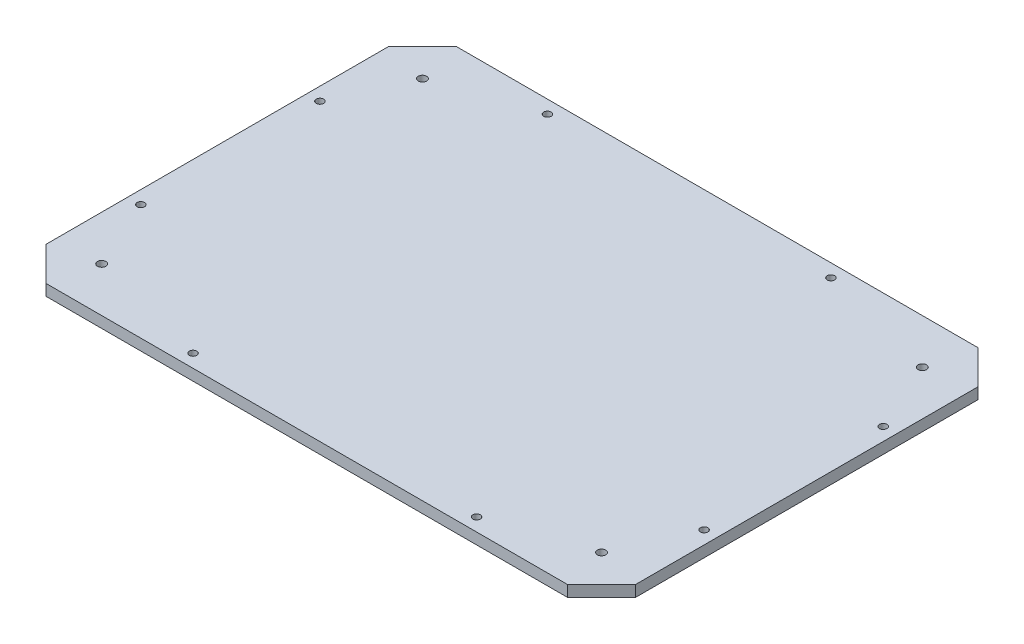
SolidWorks part; units mm, degrees
ref_plane "Front Plane" through (0, 0, 0) normal (0, 0, 1) x (1, 0, 0)
ref_plane "Top Plane" through (0, 0, 0) normal (0, 1, 0) x (1, 0, 0)
ref_plane "Right Plane" through (0, 0, 0) normal (1, 0, 0) x (0, 0, -1)
sketch "Sketch1" plane through (0, 0, 0) normal (0, 1, 0) x (1, 0, 0)
  line L1 (8.4883, 0) -> (510.1383, 0)
  line L2 (8.4883, 0) -> (8.4883, -349.25)
  line L3 (8.4883, -349.25) -> (510.1383, -349.25)
  line L4 (510.1383, 0) -> (510.1383, -349.25)
  dimension "D1" = 501.65
  dimension "D2" = 349.25
extrude "Boss-Extrude1" add sketch "Sketch1" along normal blind 9.525
sketch "Sketch2" plane through (0, 9.525, 0) normal (0, 1, 0) x (1, 0, 0)
  circle A0 centre (392.6633, -338.1375) radius 3.175
  circle A1 centre (151.3633, -338.1375) radius 3.175
  circle A2 centre (367.2633, -11.1125) radius 3.175
  circle A3 centre (125.9633, -11.1125) radius 3.175
  circle A4 centre (19.6008, -250.825) radius 3.175
  circle A5 centre (19.6008, -98.425) radius 3.175
  circle A6 centre (499.0258, -250.825) radius 3.175
  circle A7 centre (499.0258, -98.425) radius 3.175
extrude "Cut-Extrude1" cut sketch "Sketch2" against normal up to surface (9.525 mm away) up to face at (259.3133, 0, 174.625)
sketch "Sketch3" plane through (0, 9.525, 0) normal (0, 1, 0) x (1, 0, 0)
  line L0 (472.0383, -349.25) -> (472.0383, 3.175) construction
  line L1 (510.1383, -349.25) -> (8.4883, -349.25) construction
  line L2 (513.3133, 3.175) -> (5.3133, 3.175) construction
  line L3 (510.1383, 0) -> (510.1383, -349.25) construction
  line L4 (46.5883, -349.25) -> (46.5883, 0) construction
  line L5 (8.4883, 0) -> (510.1383, 0) construction
  line L6 (8.4883, -349.25) -> (8.4883, 0) construction
  line L7 (510.1383, -311.15) -> (8.4883, -311.15) construction
  line L8 (510.1383, -38.1) -> (8.4883, -38.1) construction
  point P18 (472.0383, -311.15)
  point P19 (472.0383, -38.1)
  point P20 (46.5883, -38.1)
  point P21 (46.5883, -311.15)
  dimension "D1" = 38.1
  dimension "D2" = 38.1
  dimension "D3" = 38.1
  dimension "D4" = 38.1
sketch "Sketch4" plane through (0, 9.525, 0) normal (0, 1, 0) x (1, 0, 0)
  circle A0 centre (472.0383, -38.1) radius 3.5719
  circle A1 centre (472.0383, -311.15) radius 3.5719
  circle A2 centre (46.5883, -311.15) radius 3.5719
  circle A3 centre (46.5883, -38.1) radius 3.5719
  dimension "D1" = 7.1437
  dimension "D2" = 7.1437
  dimension "D3" = 7.1437
  dimension "D4" = 7.1437
extrude "Cut-Extrude2" cut sketch "Sketch4" against normal up to surface (9.525 mm away) up to face at (499.0258, 0, 101.6)
chamfer "Chamfer1" distance 2.921 angle 42 4 edges at (46.5883, 0, 314.7219) (46.5883, 0, 41.6719) (472.0383, 0, 41.6719) (472.0383, 0, 314.7219)
sketch "Sketch5" plane through (0, 9.525, 0) normal (0, 1, 0) x (1, 0, 0)
  line L0 (37.3137, 0) -> (8.4883, -28.8255)
  line L1 (510.1383, 0) -> (8.4883, 0) construction
  line L2 (8.4883, 0) -> (8.4883, -349.25) construction
  line L3 (8.4883, -28.8255) -> (8.4883, 0)
  line L4 (8.4883, 0) -> (37.3137, 0)
  line L5 (259.3133, 0) -> (259.3133, -349.25) construction
  line L6 (8.4883, -349.25) -> (510.1383, -349.25) construction
  line L7 (8.4883, -174.625) -> (510.1383, -174.625) construction
  line L8 (510.1383, -349.25) -> (510.1383, 0) construction
  line L9 (510.1383, -28.8255) -> (510.1383, 0)
  line L10 (510.1383, 0) -> (481.3128, 0)
  line L11 (481.3128, 0) -> (510.1383, -28.8255)
  line L12 (481.3128, -349.25) -> (510.1383, -320.4245)
  line L13 (510.1383, -320.4245) -> (510.1383, -349.25)
  line L14 (510.1383, -349.25) -> (481.3128, -349.25)
  line L15 (8.4883, -320.4245) -> (8.4883, -349.25)
  line L16 (8.4883, -349.25) -> (37.3137, -349.25)
  line L17 (37.3137, -349.25) -> (8.4883, -320.4245)
  dimension "D1" = 45
  dimension "D2" = 45
extrude "Cut-Extrude3" cut sketch "Sketch5" against normal up to surface (9.525 mm away) up to face at (46.5883, 0, 317.6429)
